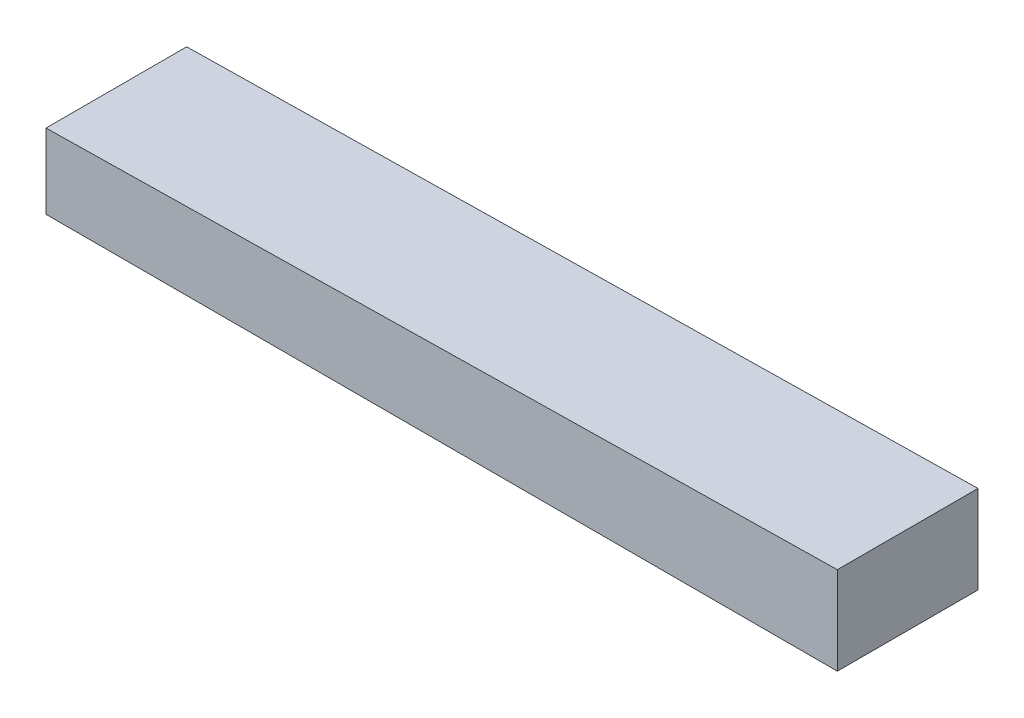
SolidWorks part; units mm, degrees
material "AISI 1035 Steel (SS)"
ref_plane "Front Plane" through (0, 0, 0) normal (0, 0, 1) x (1, 0, 0)
ref_plane "Top Plane" through (0, 0, 0) normal (0, 1, 0) x (1, 0, 0)
ref_plane "Right Plane" through (0, 0, 0) normal (1, 0, 0) x (0, 0, -1)
sketch "Sketch2" plane through (0, 0, 0) normal (0, 0, 1) x (1, 0, 0)
  line L0 (-45, 0) -> (45, 0)
  line L5 (45, 0) -> (45, 10)
  line L6 (-45, 0) -> (-45, 8.5)
  line L7 (-45, 8.5) -> (45, 10)
  point P4 (0, 0)
  dimension "D1" = 90
  dimension "D2" = 10
  dimension "D3" = 8.5
extrude "Boss-Extrude1" add sketch "Sketch2" along normal blind 16
